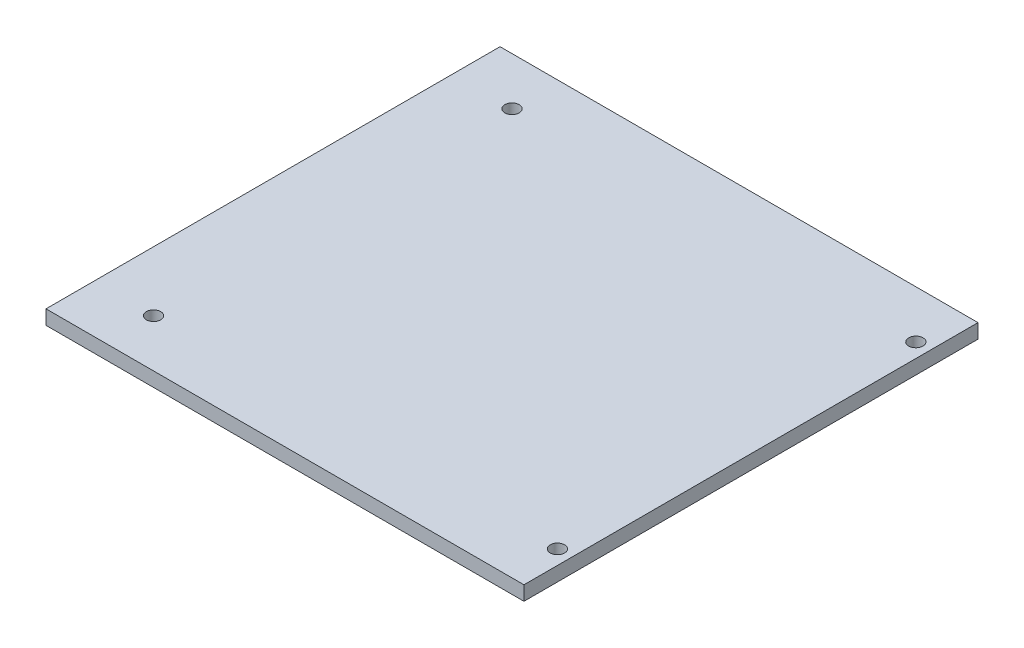
SolidWorks part; units mm, degrees
ref_plane "Front Plane" through (0, 0, 0) normal (0, 0, 1) x (1, 0, 0)
ref_plane "Top Plane" through (0, 0, 0) normal (0, 1, 0) x (1, 0, 0)
ref_plane "Right Plane" through (0, 0, 0) normal (1, 0, 0) x (0, 0, -1)
sketch "Sketch1" plane through (0, 0, 0) normal (0, 1, 0) x (1, 0, 0)
  line L1 (50, -47.5) -> (-50, -47.5)
  line L2 (50, -47.5) -> (50, 47.5)
  line L3 (50, 47.5) -> (-50, 47.5)
  line L4 (-50, -47.5) -> (-50, 47.5)
  line L5 (50, -47.5) -> (-50, 47.5) construction
  line L6 (50, 47.5) -> (-50, -47.5) construction
  circle A0 centre (-37.5, 37.5) radius 1.5
  circle A1 centre (47, 37.5) radius 1.5
  circle A2 centre (47, -37.5) radius 1.5
  circle A3 centre (-37.5, -37.5) radius 1.5
  point P0 (0, 0)
  dimension "D3" = 3
  dimension "D4" = 10
  dimension "D6" = 3
  dimension "D9" = 10
  dimension "D10" = 3
  dimension "D11" = 12.5
  dimension "D12" = 10
  dimension "D1" = 100
  dimension "D2" = 95
  dimension "D5" = 12.5
  dimension "D7" = 10
  dimension "D8" = 3
extrude "Boss-Extrude1" add sketch "Sketch1" along normal blind 3
